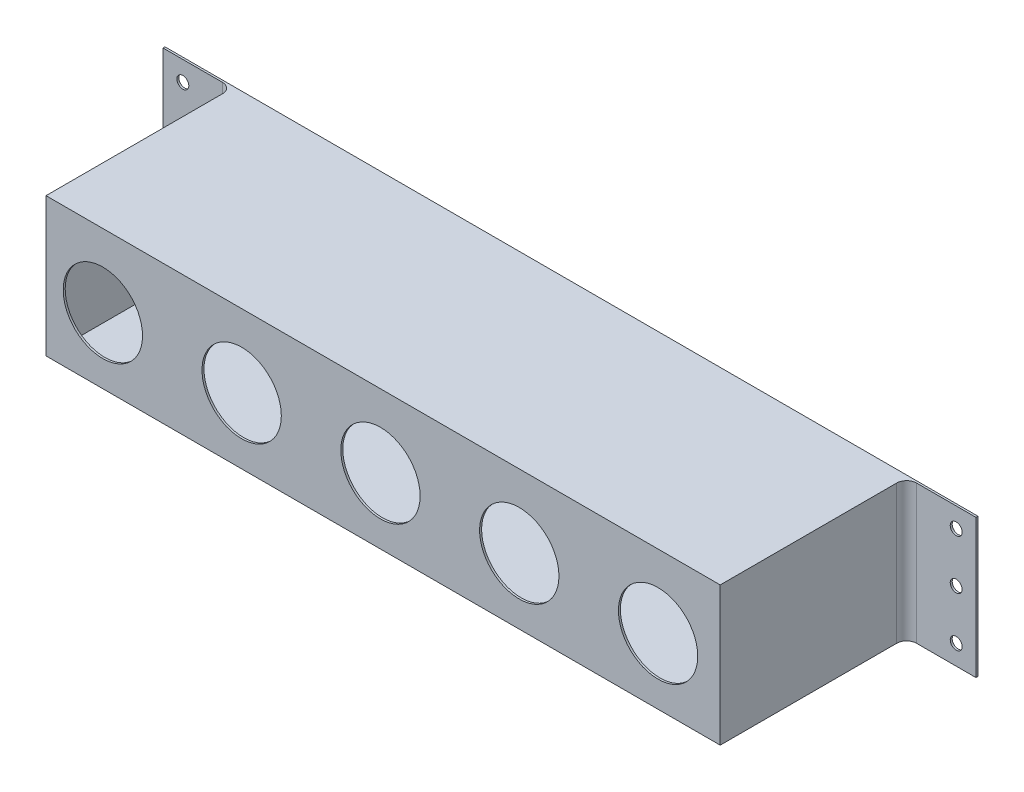
SolidWorks part; units mm, degrees
material "锻制不锈钢"
ref_plane "前视基准面" through (0, 0, 0) normal (0, 0, 1) x (1, 0, 0)
ref_plane "上视基准面" through (0, 0, 0) normal (0, 1, 0) x (1, 0, 0)
ref_plane "右视基准面" through (0, 0, 0) normal (1, 0, 0) x (0, 0, -1)
sketch "草图1" plane through (0, 0, 0) normal (0, 0, 1) x (1, 0, 0)
  line L1 (-205, -35) -> (205, -35)
  line L2 (-205, -35) -> (-205, 35)
  line L3 (-205, 35) -> (205, 35)
  line L4 (205, -35) -> (205, 35)
  line L5 (-205, -35) -> (205, 35) construction
  line L6 (-205, 35) -> (205, -35) construction
  point P0 (0, 0)
  dimension "D1" = 410
  dimension "D2" = 70
extrude "凸台-拉伸1" add sketch "草图1" along normal blind 95
sketch "草图2" plane through (0, 35, 0) normal (0, 1, 0) x (1, 0, 0)
  line L0 (205, -95) -> (170, -95)
  line L1 (205, -95) -> (-205, -95) construction
  line L2 (170, -95) -> (170, -1)
  line L3 (170, -1) -> (205, -1)
  line L4 (205, -95) -> (205, 0) construction
  line L5 (205, -1) -> (205, -95)
  line L6 (0, 0) -> (0, -95) construction
  line L7 (205, 0) -> (-205, 0) construction
  line L8 (-205, -1) -> (-205, -95)
  line L9 (-170, -1) -> (-205, -1)
  line L10 (-170, -95) -> (-170, -1)
  line L11 (-205, -95) -> (-170, -95)
  dimension "D1" = 1
  dimension "D3" = 35
extrude "切除-拉伸1" cut sketch "草图2" against normal blind 95
shell "抽壳1" thickness 1
fillet "圆角2" radius 5 2 edges at (170, 0, 1) (-170, 0, 1)
sketch "草图3" plane through (0, 0, 1) normal (0, 0, 1) x (1, 0, 0)
  line L0 (0, 35) -> (0, -35) construction
  line L1 (170, 35) -> (-170, 35) construction
  line L2 (-170, -35) -> (170, -35) construction
  line L3 (205, 0) -> (175, 0) construction
  line L4 (205, -35) -> (205, 35) construction
  line L5 (175, 35) -> (175, -35) construction
  line L6 (205, 35) -> (175, 35) construction
  line L7 (195, 25) -> (195, -25) construction
  circle A0 centre (195, 25) radius 3
  circle A1 centre (195, -25) radius 3
  circle A2 centre (195, 0) radius 3
  circle A3 centre (-195, 0) radius 3
  circle A4 centre (-195, 25) radius 3
  circle A5 centre (-195, -25) radius 3
  dimension "D1" = 6
  dimension "D4" = 6
  dimension "D2" = 10
  dimension "D3" = 10
extrude "切除-拉伸2" cut sketch "草图3" against normal through all
sketch "草图4" plane through (0, 0, 95) normal (0, 0, 1) x (1, 0, 0)
  line L0 (-170, -1.84) -> (170, -1.84) construction
  line L1 (-170, 35) -> (-170, -35) construction
  line L5 (-175, -35) -> (-205, -35) construction
  circle A0 centre (-141.33, -1.84) radius 20
  circle A1 centre (-71.33, -1.84) radius 20
  circle A2 centre (-1.33, -1.84) radius 20
  circle A3 centre (68.67, -1.84) radius 20
  circle A4 centre (138.67, -1.84) radius 20
  dimension "D1" = 40
  dimension "D2" = 28.67
  dimension "D4" = 33.16
  dimension "D3" = 5
extrude "切除-拉伸3" cut sketch "草图4" against normal through all
sketch "草图6" plane through (0, -35, 0) normal (0, -1, 0) x (1, 0, 0)
  line L2 (-205, 0) -> (205, 0) construction
  spline S0 degree 3 poles (-40.9118, -26.743) (-67.0321, 17.5679) (-11.123, 39.8258) (8.2857, 94.9226) (65.2507, 98.8214) (149.1496, 133.6567) (145.1008, 87.9541) (158.0558, 60.9347) (166.0236, 17.1901) (108.959, -7.0874) (161.2411, -19.6498) (71.4813, -17.4741) (40.2958, -19.0884) (-3.6297, -16.0571) (-40.9118, -26.743) (-67.0321, 17.5679) (-11.123, 39.8258) knots -0.164031 -0.10733 -0.029719 0 0.11514 0.175782 0.279018 0.417607 0.428717 0.500609 0.570883 0.636274 0.659094 0.753097 0.835969 0.89267 0.970281 1 1.11514 1.175782 1.279018 only from (-54.6281, 0) to (-54.6281, 0)
extrude "切除-拉伸6" [suppressed] cut sketch "草图6" against normal up to surface (1 mm away)
